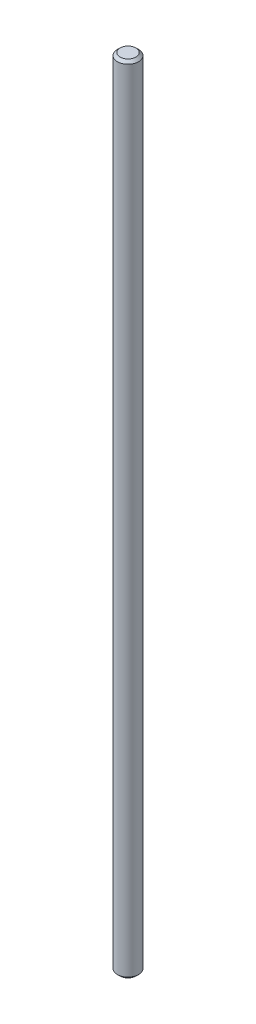
SolidWorks part; units mm, degrees
material "1060 Alloy"
ref_plane "Front Plane" through (0, 0, 0) normal (0, 0, 1) x (1, 0, 0)
ref_plane "Top Plane" through (0, 0, 0) normal (0, 1, 0) x (1, 0, 0)
ref_plane "Right Plane" through (0, 0, 0) normal (1, 0, 0) x (0, 0, -1)
sketch "Sketch1" plane through (0, 0, 0) normal (0, 1, 0) x (1, 0, 0)
  circle A0 centre (0, 0) radius 4
  dimension "D1" = 8
extrude "Boss-Extrude1" add sketch "Sketch1" along normal blind 300 contours A0
chamfer "Chamfer1" distance 1 angle 45 2 edges at (0, 0, 4) (0, 300, 4)
